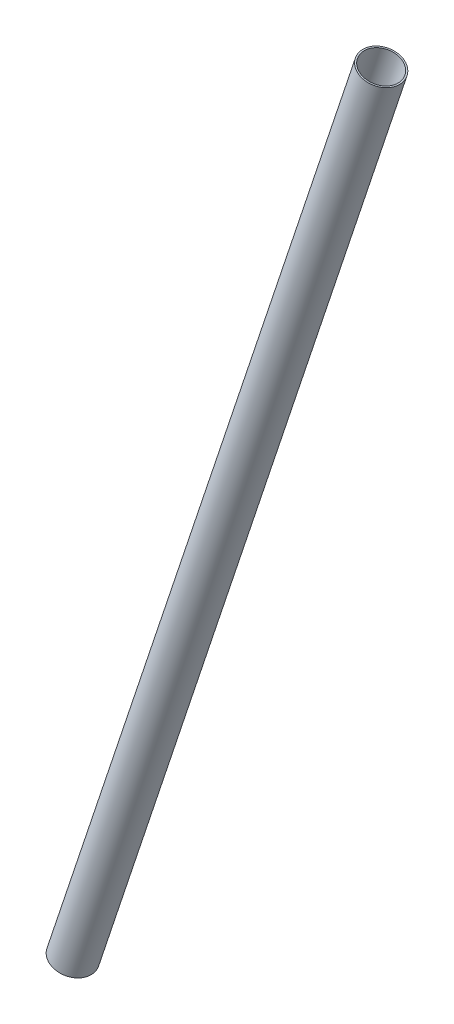
SolidWorks part; units mm, degrees
ref_plane "Alzado" through (0, 0, 0) normal (0, 0, 1) x (1, 0, 0)
ref_plane "Planta" through (0, 0, 0) normal (0, 1, 0) x (1, 0, 0)
ref_plane "Vista lateral" through (0, 0, 0) normal (1, 0, 0) x (0, 0, -1)
sketch "Croquis1" plane through (0, 0, 0) normal (0, 0, 1) x (1, 0, 0)
  line L1 (400, 1200) -> (400, 0) construction
  line L2 (0, 0) -> (400, 0) construction
  line L14 (0, 0) -> (21.4192, -16.0644) construction
  line L16 (285.8686, 777.284) -> (426.774, 1200) construction
  line L19 (426.774, 1200) -> (424.8766, 1200.6325) construction
  line L20 (400, 1200) -> (0, 0) construction
  line L21 (426.774, 1200) -> (400, 1200) construction
  line L22 (426.774, 1200) -> (21.4192, -16.0644)
  line L25 (424.8766, 1200.6325) -> (426.774, 1200)
  line L29 (-26.774, 0) -> (21.4192, -16.0644) construction
  line L30 (19.5218, -15.4319) -> (21.4192, -16.0644) construction
  line L31 (424.8766, 1200.6325) -> (19.5218, -15.4319)
  line L32 (19.5218, -15.4319) -> (21.4192, -16.0644)
  line L33 (0, 0) -> (-2.6774, -8.0322) construction
  line L34 (-26.774, 0) -> (0, 0) construction
  line L35 (426.774, 1200) -> (402.6774, 1208.0322) construction
  line L36 (400, 1200) -> (402.6774, 1208.0322) construction
  dimension "D1" = 1200
  dimension "D2" = 400
  dimension "D3" = 90
  dimension "D4" = 90
  dimension "D5" = 90
  dimension "D6" = 50.8
  dimension "D7" = 2
  dimension "D8" = 90
  dimension "D9" = 71.565
  dimension "D10" = 90
revolve "Revolución1" add sketch "Croquis1" angle 360 about L20
ref_plane "Plano2" through (707.11, 0, 0) normal (1, 0, 0) x (0, 0, -1)
sketch "Croquis6" plane through (0, 0, 0) normal (0, 0, 1) x (1, 0, 0)
  point P0 (21.4192, -16.0644)
sketch "Croquis8" plane through (0, 0, 0) normal (0, 0, 1) x (1, 0, 0)
  line L0 (-26.774, 0) -> (21.4192, -16.0644) construction
  line L1 (424.8766, 1200.6325) -> (380.4782, 1215.4319) construction
  line L2 (426.774, 1200) -> (378.5808, 1216.0644) construction
  line L3 (378.5808, 1216.0644) -> (426.774, 1200)
  line L4 (21.4192, -16.0644) -> (-26.774, 0)
  arc A0 (21.4192, -16.0644) -> (-26.774, 0) centre (-2.6774, -8.0322) ccw
  arc A1 (378.5808, 1216.0644) -> (426.774, 1200) centre (402.6774, 1208.0322) ccw
extrude "Cortar-Extruir1" [suppressed] cut sketch "Croquis8" against normal through all and the other way through all
ref_plane "Plano3" through (0, 0, 0) normal (-0.9487, 0.3162, 0) x (-0.3162, -0.9487, 0)
